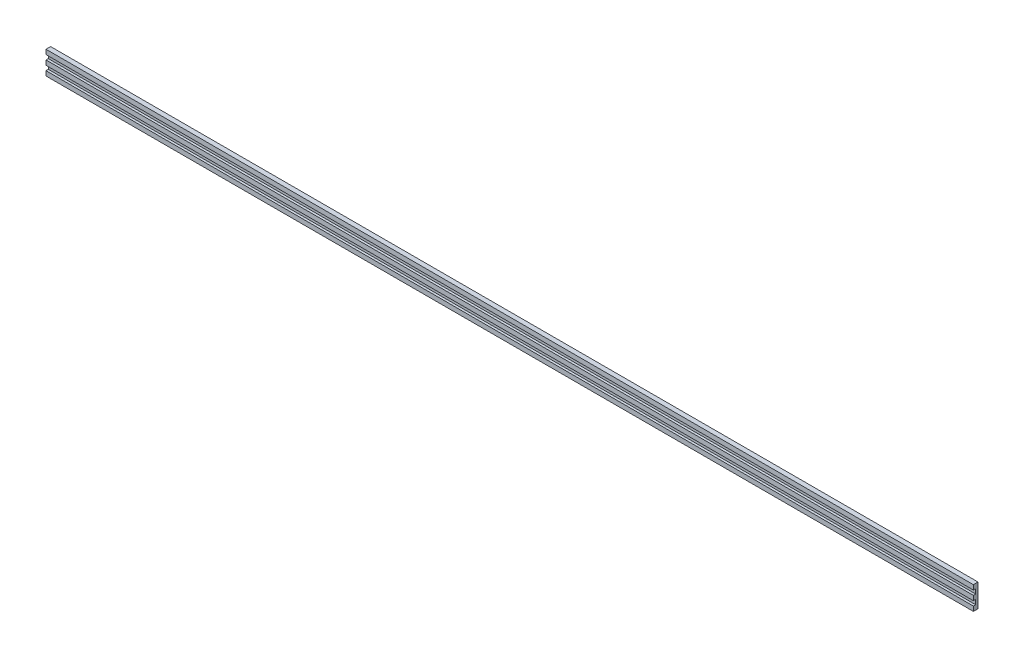
SolidWorks part; units mm, degrees
ref_plane "Front Plane" through (0, 0, 0) normal (0, 0, 1) x (1, 0, 0)
ref_plane "Top Plane" through (0, 0, 0) normal (0, 1, 0) x (1, 0, 0)
ref_plane "Right Plane" through (0, 0, 0) normal (1, 0, 0) x (0, 0, -1)
sketch "Sketch1" plane through (0, 0, 0) normal (0, 0, 1) x (1, 0, 0)
  line L1 (-100, 2.5) -> (100, 2.5)
  line L2 (-100, 2.5) -> (-100, -2.5)
  line L3 (-100, -2.5) -> (100, -2.5)
  line L4 (100, 2.5) -> (100, -2.5)
  line L5 (-100, 2.5) -> (100, -2.5) construction
  line L6 (-100, -2.5) -> (100, 2.5) construction
  point P0 (0, 0)
  dimension "D1" = 5
  dimension "D2" = 200
extrude "Boss-Extrude1" add sketch "Sketch1" along normal blind 0.5
sketch "Sketch2" plane through (0, 0, 0.5) normal (0, 0, 1) x (1, 0, 0)
  line L0 (100, -2.5) -> (100, 2.5) construction
  line L1 (-100, 2.5) -> (100, 2.5)
  line L2 (-100, 2.5) -> (-100, 1.5)
  line L3 (-100, 1.5) -> (100, 1.5)
  line L4 (100, 2.5) -> (100, 1.5)
  line L5 (-100, 2.5) -> (-100, -2.5) construction
  line L6 (-100, 0.5) -> (100, 0.5)
  line L7 (-100, 0.5) -> (-100, -0.5)
  line L8 (-100, -0.5) -> (100, -0.5)
  line L9 (100, 0.5) -> (100, -0.5)
  line L11 (-100, -2.5) -> (100, -2.5)
  line L12 (-100, -2.5) -> (-100, -1.5)
  line L13 (-100, -1.5) -> (100, -1.5)
  line L14 (100, -2.5) -> (100, -1.5)
  dimension "D1" = 1
  dimension "D2" = 1
  dimension "D3" = 1
  dimension "D4" = 1
  dimension "D5" = 1
extrude "Boss-Extrude2" add sketch "Sketch2" along normal blind 0.5
